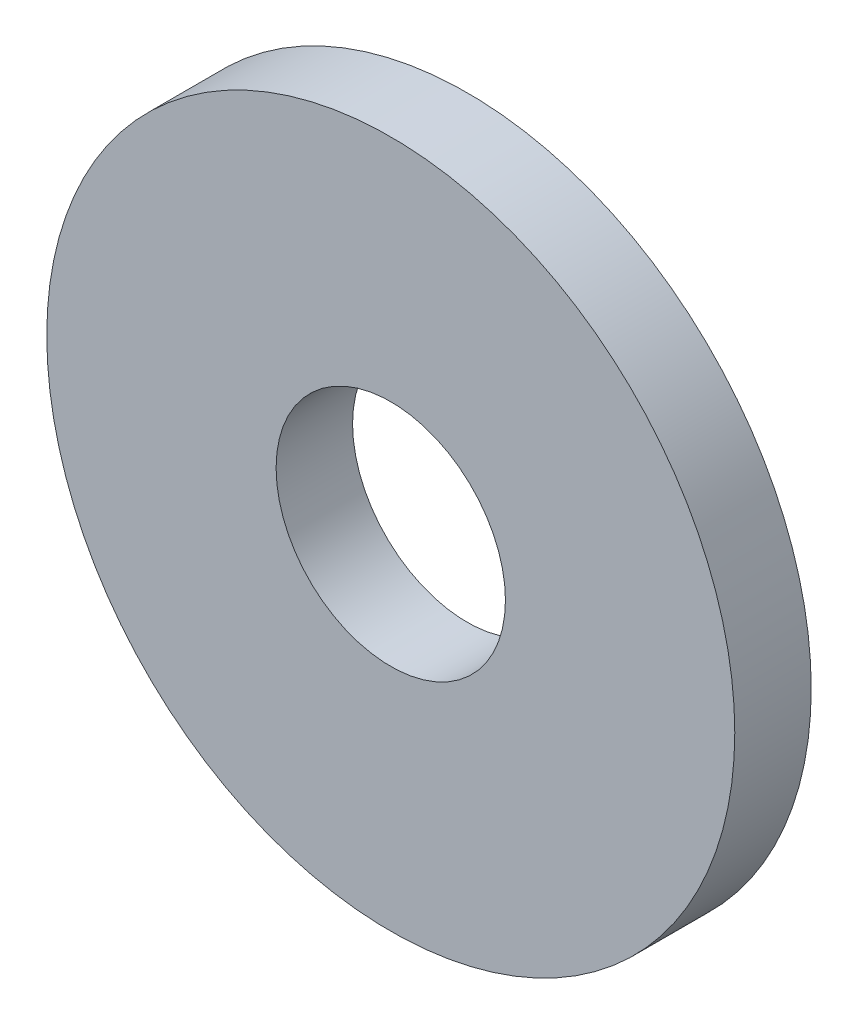
SolidWorks part; units mm, degrees
ref_plane "Front Plane" through (0, 0, 0) normal (0, 0, 1) x (1, 0, 0)
ref_plane "Top Plane" through (0, 0, 0) normal (0, 1, 0) x (1, 0, 0)
ref_plane "Right Plane" through (0, 0, 0) normal (1, 0, 0) x (0, 0, -1)
sketch "Sketch1" plane through (0, 0, 0) normal (0, 0, 1) x (1, 0, 0)
  circle A0 centre (0, 0) radius 0.75
  circle A1 centre (0, 0) radius 2.25
  dimension "D1" = 1.5
  dimension "D2" = 1.5
extrude "Boss-Extrude1" add sketch "Sketch1" along normal blind 0.5
